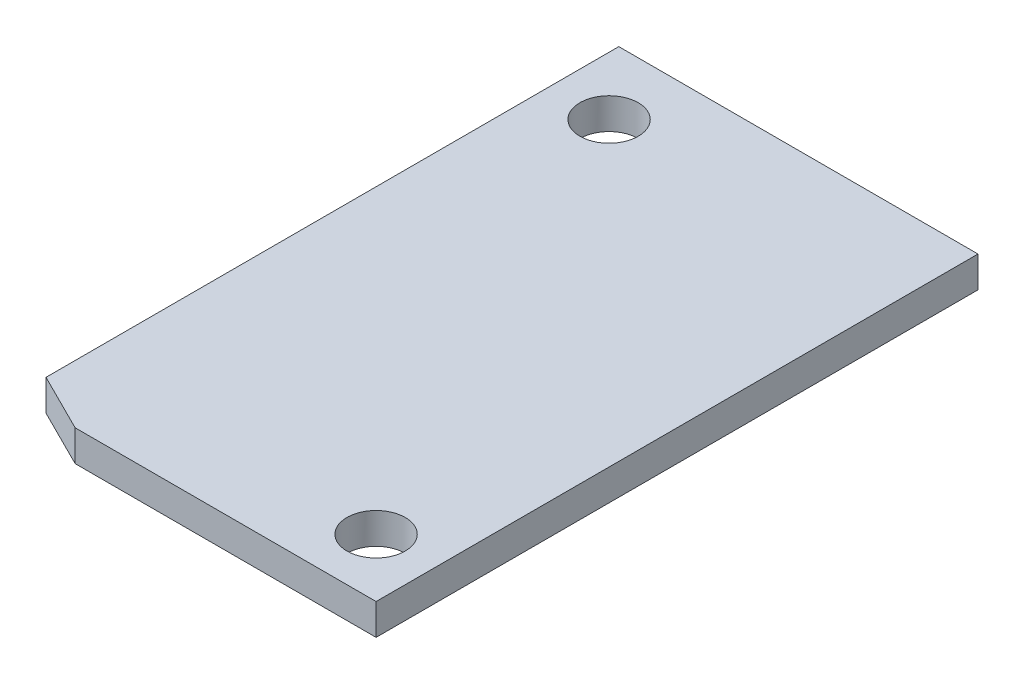
SolidWorks part; units mm, degrees
ref_plane "Front Plane" through (0, 0, 0) normal (0, 0, 1) x (1, 0, 0)
ref_plane "Top Plane" through (0, 0, 0) normal (0, 1, 0) x (1, 0, 0)
ref_plane "Right Plane" through (0, 0, 0) normal (1, 0, 0) x (0, 0, -1)
sketch "Sketch1" plane through (0, 0, 0) normal (0, 1, 0) x (1, 0, 0)
  line L0 (9.25, -15.5) -> (-9.25, 15.5) construction
  line L1 (-6.25, -15.5) -> (9.25, -15.5)
  line L2 (-9.25, -14) -> (-9.25, 15.5)
  line L3 (-9.25, 15.5) -> (9.25, 15.5)
  line L4 (9.25, -15.5) -> (9.25, 15.5)
  line L6 (-9.25, -14) -> (-6.25, -15.5)
  point P4 (0, 0)
  dimension "D1" = 18.5
  dimension "D2" = 31
  dimension "D3" = 1.5
  dimension "D4" = 3
extrude "Extrude1" add sketch "Sketch1" along normal blind 1.6
hole_wizard "Ø3.0 (3) Diameter Hole1" positions "3DSketch1" profile "Sketch2" hole size "Ø3.0" standard "DIN"
sketch3d "3DSketch1"
  line L0 (-6.25, 1.6, 15.5) -> (9.25, 1.6, 15.5) construction
  line L1 (9.25, 1.6, 15.5) -> (9.25, 1.6, -15.5) construction
  line L2 (-9.25, 1.6, -15.5) -> (-9.25, 1.6, 14) construction
  line L3 (9.25, 1.6, -15.5) -> (-9.25, 1.6, -15.5) construction
  point P0 (6.25, 1.6, 12.5)
  point P2 (-6.25, 1.6, -12)
  dimension "D1" = 3
  dimension "D2" = 3
  dimension "D3" = 3
  dimension "D4" = 3.5
sketch "Sketch2" plane through (6.25, 1.6, 12.5) normal (1, 0, 0) x (0, 0, 1)
  line L0 (0, 0) -> (0, 10.9013)
  line L1 (0, 10.9013) -> (1.5, 10)
  line L2 (1.5, 10) -> (1.5, 0)
  line L5 (1.5, 0) -> (0, 0)
  line L10 (0, 10.9013) -> (-1.5, 10) construction
  line L11 (0, -6.35) -> (0, 107.95) construction
  dimension "Hole Dia." = 3
  dimension "Hole Depth" = 10
  dimension "Drill Angle" = 118
